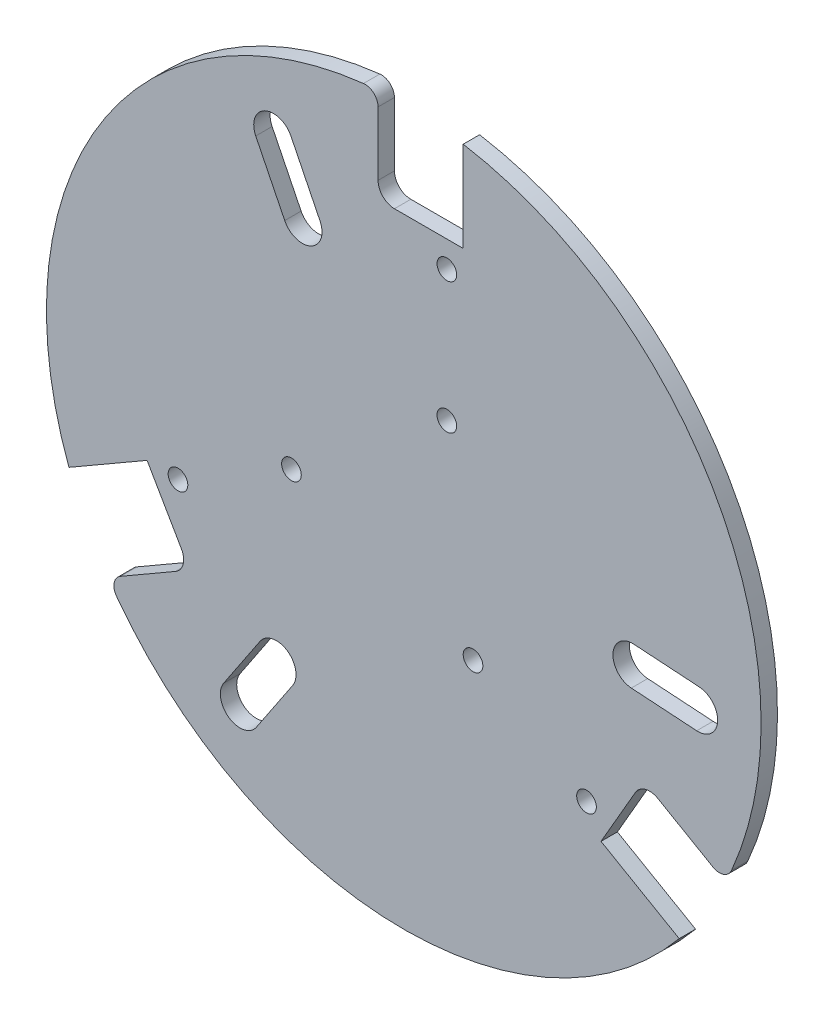
SolidWorks part; units mm, degrees
ref_plane "Front Plane" through (0, 0, 0) normal (0, 0, 1) x (1, 0, 0)
ref_plane "Top Plane" through (0, 0, 0) normal (0, 1, 0) x (1, 0, 0)
ref_plane "Right Plane" through (0, 0, 0) normal (1, 0, 0) x (0, 0, -1)
sketch "Sketch1" plane through (0, 0, 0) normal (0, 0, 1) x (1, 0, 0)
  line L0 (0, 50.8) -> (0, 0) construction
  line L1 (0, 0) -> (43.9941, -25.4) construction
  line L2 (0, 0) -> (-43.9941, -25.4) construction
  line L3 (0, 0) -> (43.9941, 25.4) construction
  line L4 (0, 0) -> (-43.9941, 25.4) construction
  line L5 (0, 0) -> (0, -50.8) construction
  line L6 (-64.912, -24.1702) -> (-49.7561, -15.4199)
  line L7 (-49.7561, -15.4199) -> (-46.5811, -20.9192)
  line L8 (-4.986, 69.0863) -> (-4.986, 53.975)
  line L9 (53.3881, -44.1304) -> (38.2321, -35.3801)
  line L10 (38.2321, -35.3801) -> (41.4071, -29.8808)
  line L11 (-1.811, 50.8) -> (5.174, 50.8)
  line L12 (-57.3375, -38.8612) -> (-44.2507, -31.3055)
  line L13 (5.174, 50.8) -> (11.524, 50.8)
  line L14 (11.524, 50.8) -> (11.524, 68.3006)
  line L15 (-43.0886, -26.9684) -> (-46.5811, -20.9192)
  line L16 (62.3235, -30.2251) -> (49.2367, -22.6695)
  line L17 (44.8996, -23.8316) -> (41.4071, -29.8808)
  line L18 (-39.5947, -22.86) -> (-43.7692, -15.6296) construction
  line L19 (-43.7692, -15.6296) -> (-21.7721, -2.9296) construction
  line L20 (-21.7721, -2.9296) -> (-17.5976, -10.16) construction
  line L21 (17.5976, -10.16) -> (13.4231, -17.3904) construction
  line L22 (13.4231, -17.3904) -> (35.4202, -30.0904) construction
  line L23 (35.4202, -30.0904) -> (39.5947, -22.86) construction
  line L24 (0, 45.72) -> (8.349, 45.72) construction
  line L25 (8.349, 45.72) -> (8.349, 20.32) construction
  line L26 (8.349, 20.32) -> (0, 20.32) construction
  line L27 (-25.2777, 51.2558) -> (-19.6604, 39.8656) construction
  line L28 (-21.8606, 52.941) -> (-16.2434, 41.5508)
  line L29 (-28.6948, 49.5707) -> (-23.0775, 38.1805)
  line L30 (57.0277, -3.7368) -> (44.3549, -2.9064) construction
  line L31 (56.7786, -7.5386) -> (44.1058, -6.7082)
  line L32 (57.2768, 0.0651) -> (44.604, 0.8955)
  line L33 (-31.75, -47.519) -> (-24.6944, -36.9593) construction
  line L34 (-34.9179, -45.4024) -> (-27.8624, -34.8426)
  line L35 (-28.5821, -49.6357) -> (-21.5265, -39.0759)
  circle A0 centre (0, 0) radius 50.8 construction
  circle A1 centre (0, 45.72) radius 1.397 construction
  circle A2 centre (0, 20.32) radius 1.397 construction
  circle A3 centre (39.5947, -22.86) radius 1.397 construction
  circle A4 centre (17.5976, -10.16) radius 1.397 construction
  circle A5 centre (-39.5947, -22.86) radius 1.397 construction
  circle A6 centre (-17.5976, -10.16) radius 1.397 construction
  circle A7 centre (0, 0) radius 57.15 construction
  circle A8 centre (-25.2777, 51.2558) radius 3.175 construction
  circle A9 centre (57.0277, -3.7368) radius 3.175 construction
  circle A10 centre (-31.75, -47.519) radius 3.175 construction
  arc A11 (-57.3375, -38.8612) -> (53.3881, -44.1304) centre (0, 0) ccw
  arc A12 (62.3235, -30.2251) -> (11.524, 68.3006) centre (0, 0) ccw
  arc A13 (-21.8606, 52.941) -> (-28.6948, 49.5707) centre (-25.2777, 51.2558) ccw
  arc A14 (-4.986, 53.975) -> (-1.811, 50.8) centre (-1.811, 53.975) ccw
  arc A15 (-44.2507, -31.3055) -> (-43.0886, -26.9684) centre (-45.8382, -28.5559) ccw
  arc A16 (49.2367, -22.6695) -> (44.8996, -23.8316) centre (47.6492, -25.4191) ccw
  circle A17 centre (-43.7692, -15.6296) radius 1.905
  circle A18 centre (-21.7721, -2.9296) radius 1.905
  circle A19 centre (13.4231, -17.3904) radius 1.905
  circle A20 centre (35.4202, -30.0904) radius 1.905
  circle A21 centre (8.349, 45.72) radius 1.905
  circle A22 centre (8.349, 20.32) radius 1.905
  arc A23 (-23.0775, 38.1805) -> (-16.2434, 41.5508) centre (-19.6604, 39.8656) ccw
  arc A24 (-4.986, 69.0863) -> (-64.912, -24.1702) centre (0, 0) ccw
  arc A25 (56.7786, -7.5386) -> (57.2768, 0.0651) centre (57.0277, -3.7368) ccw
  arc A26 (44.604, 0.8955) -> (44.1058, -6.7082) centre (44.3549, -2.9064) ccw
  arc A27 (-34.9179, -45.4024) -> (-28.5821, -49.6357) centre (-31.75, -47.519) ccw
  arc A28 (-21.5265, -39.0759) -> (-27.8624, -34.8426) centre (-24.6944, -36.9593) ccw
  point P39 (-48.1686, -18.1696)
  point P42 (39.8196, -32.6304)
  point P43 (8.349, 50.8)
  point P64 (-22.4691, 45.5607)
  point P70 (50.6913, -3.3216)
  point P76 (-28.2222, -42.2392)
  dimension "D1" = 101.6
  dimension "D4" = 25.4
  dimension "D5" = 25.4
  dimension "D6" = 25.4
  dimension "D10" = 2.794
  dimension "D11" = 6.35
  dimension "D12" = 31.75
  dimension "D13" = 114.3
  dimension "D16" = 17.5006
  dimension "D21" = 3.175
  dimension "D22" = 8.349
  dimension "D23" = 3.81
  dimension "D27" = 3.81
  dimension "D2" = 120
  dimension "D3" = 120
  dimension "D7" = 5.08
  dimension "D8" = 5.08
  dimension "D9" = 5.08
  dimension "D14" = 31.75
  dimension "D15" = 31.75
  dimension "D17" = 6.35
  dimension "D18" = 16.51
  dimension "D19" = 16.51
  dimension "D20" = 16.51
  dimension "D24" = 8.349
  dimension "D25" = 8.349
  dimension "D26" = 12.7
extrude "Boss-Extrude1" add sketch "Sketch1" along normal blind 3.175
fillet "Fillet1" radius 2.54 3 edges at (62.3235, -30.2251, 1.5875) (-57.3375, -38.8612, 1.5875) (-4.986, 69.0863, 1.5875)
